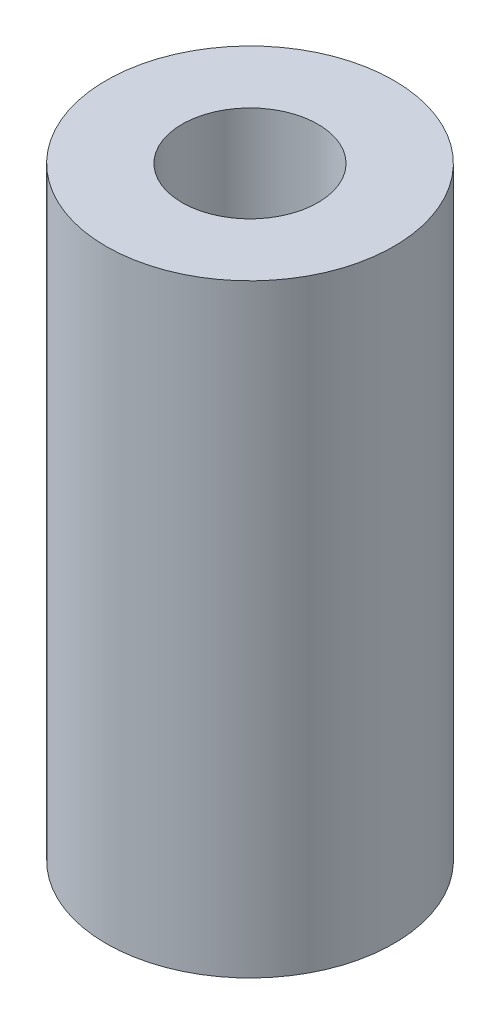
SolidWorks part; units mm, degrees
ref_plane "Front Plane" through (0, 0, 0) normal (0, 0, 1) x (1, 0, 0)
ref_plane "Top Plane" through (0, 0, 0) normal (0, 1, 0) x (1, 0, 0)
ref_plane "Right Plane" through (0, 0, 0) normal (1, 0, 0) x (0, 0, -1)
sketch "Sketch1" plane through (0, 0, 0) normal (0, 1, 0) x (1, 0, 0)
  circle A0 centre (0, 0) radius 4.55
  circle A1 centre (0, 0) radius 2.15
extrude "Boss-Extrude2" add sketch "Sketch1" along normal blind 19.1
